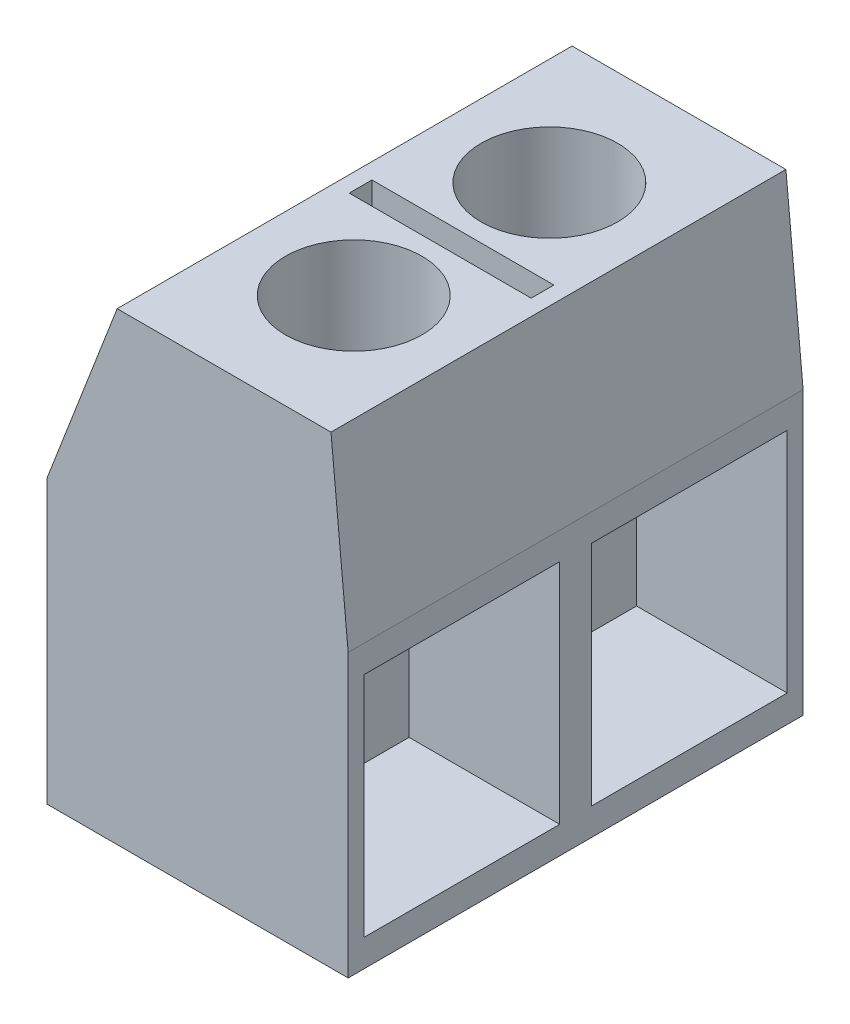
SolidWorks part; units mm, degrees
ref_plane "Front Plane" through (0, 0, 0) normal (0, 0, 1) x (1, 0, 0)
ref_plane "Top Plane" through (0, 0, 0) normal (0, 1, 0) x (1, 0, 0)
ref_plane "Right Plane" through (0, 0, 0) normal (1, 0, 0) x (0, 0, -1)
sketch "Sketch2" plane through (0, 0, 0) normal (0, 0, 1) x (1, 0, 0)
  line L0 (-3.3111, 0) -> (3.3111, 0)
  line L1 (3.3111, 0) -> (3.3111, 6.2)
  line L2 (3.3111, 6.2) -> (2.9336, 10.2022)
  line L3 (2.9336, 10.2022) -> (-1.7664, 10.2022)
  line L4 (-1.7664, 10.2022) -> (-3.3111, 6.2)
  line L5 (-3.3111, 6.2) -> (-3.3111, 0)
  point P4 (0, 0)
  dimension "D1" = 6.2
  dimension "D2" = 4.02
  dimension "D3" = 6.2
  dimension "D4" = 4.29
  dimension "D5" = 4.7
extrude "Boss-Extrude2" add sketch "Sketch2" along normal blind 10
sketch "Sketch3" plane through (0, 0, 0) normal (1, 0, 0) x (0, 0, -1)
  line L0 (-5, 0) -> (-5, 6.2) construction
  line L1 (-10, 0) -> (0, 0) construction
  line L2 (-10, 6.2) -> (0, 6.2) construction
  line L3 (-5, 3.1) -> (0, 3.1) construction
  line L4 (0, 0) -> (0, 6.2) construction
  line L5 (-5.35, 5.6) -> (-9.65, 0.6) construction
  line L6 (-4.65, 5.6) -> (-0.35, 5.6)
  line L7 (-4.65, 5.6) -> (-4.65, 0.6)
  line L8 (-4.65, 0.6) -> (-0.35, 0.6)
  line L9 (-0.35, 5.6) -> (-0.35, 0.6)
  line L10 (-4.65, 5.6) -> (-0.35, 0.6) construction
  line L11 (-4.65, 0.6) -> (-0.35, 5.6) construction
  line L12 (-5.35, 0.6) -> (-9.65, 5.6) construction
  line L13 (-5.35, 5.6) -> (-5.35, 0.6)
  line L14 (-5.35, 0.6) -> (-9.65, 0.6)
  line L15 (-9.65, 5.6) -> (-9.65, 0.6)
  line L16 (-5.35, 5.6) -> (-9.65, 5.6)
  point P10 (-2.5, 3.1)
  dimension "D1" = 4.3
  dimension "D2" = 5
extrude "Cut-Extrude3" cut sketch "Sketch3" along normal blind 4.3
ref_plane "Plane1" through (0, 10.2022, 0) normal (0, 1, 0) x (1, 0, 0)
sketch "Sketch5" plane through (0, 10.2022, 0) normal (0, 1, 0) x (1, 0, 0)
  line L0 (-1.7664, -5) -> (2.9336, -5)
  line L1 (-1.7664, -10) -> (-1.7664, 0) construction
  line L2 (2.9336, -10) -> (2.9336, 0) construction
  line L6 (-1.4164, -5.25) -> (2.5836, -5.25)
  line L7 (-1.4164, -5.25) -> (-1.4164, -4.75)
  line L8 (-1.4164, -4.75) -> (2.5836, -4.75)
  line L9 (2.5836, -5.25) -> (2.5836, -4.75)
  line L10 (-1.4164, -5.25) -> (2.5836, -4.75) construction
  line L11 (-1.4164, -4.75) -> (2.5836, -5.25) construction
  circle A0 centre (0.5836, -2.85) radius 1.5
  circle A1 centre (0.5836, -7.15) radius 1.5
  point P6 (0.5836, -5)
  dimension "D1" = 3
  dimension "D2" = 2.15
extrude "Cut-Extrude4" cut sketch "Sketch5" against normal blind 5.3 contours A1 | L6 L9 L0 L7 | L0 L9 L8 L7 | A0
